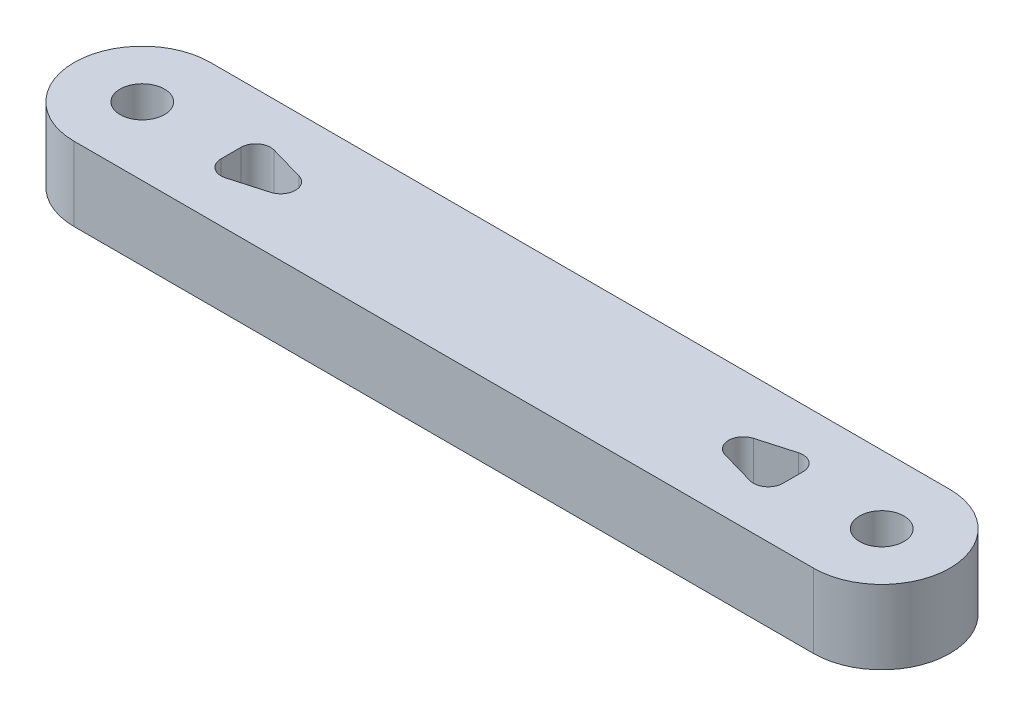
SolidWorks part; units mm, degrees
ref_plane "Front Plane" through (0, 0, 0) normal (0, 0, 1) x (1, 0, 0)
ref_plane "Top Plane" through (0, 0, 0) normal (0, 1, 0) x (1, 0, 0)
ref_plane "Right Plane" through (0, 0, 0) normal (1, 0, 0) x (0, 0, -1)
sketch "Sketch1" plane through (0, 0, 0) normal (0, 1, 0) x (1, 0, 0)
  line L0 (0, 0) -> (50, 0) construction
  line L1 (0, 0) -> (50, 0) construction
  line L2 (0, 4.6106) -> (50, 4.6106)
  line L3 (0, -4.6106) -> (50, -4.6106)
  circle A0 centre (0, 0) radius 1.5
  circle A1 centre (50, 0) radius 1.5
  arc A2 (0, 4.6106) -> (0, -4.6106) centre (0, 0) ccw
  arc A3 (50, -4.6106) -> (50, 4.6106) centre (50, 0) ccw
  point P5 (25, 0)
  dimension "D1" = 50
extrude "Boss-Extrude1" add sketch "Sketch1" along normal blind 5
sketch "Sketch3" plane through (0, 5, 0) normal (0, 1, 0) x (1, 0, 0)
  line L0 (25, 4.6106) -> (25, -4.6106) construction
  line L1 (0, 4.6106) -> (50, 4.6106) construction
  line L2 (0, -4.6106) -> (50, -4.6106) construction
  line L3 (0, 0) -> (6, 0) construction
  line L4 (6, 2) -> (6, -2)
  line L5 (6, 0) -> (13, 0) construction
  line L6 (6, -2) -> (13, 0)
  line L7 (6, 2) -> (13, 0)
  line L8 (44, 2) -> (44, -2)
  line L9 (44, -2) -> (37, 0)
  line L10 (44, 2) -> (37, 0)
  dimension "D1" = 6
  dimension "D2" = 2
  dimension "D3" = 7
extrude "Cut-Extrude2" cut sketch "Sketch3" against normal blind 17
fillet "Fillet1" radius 1 6 edges at (44, 2.5, 2) (44, 2.5, -2) (37, 2.5, 0) (13, 2.5, 0) (6, 2.5, 2) (6, 2.5, -2)
